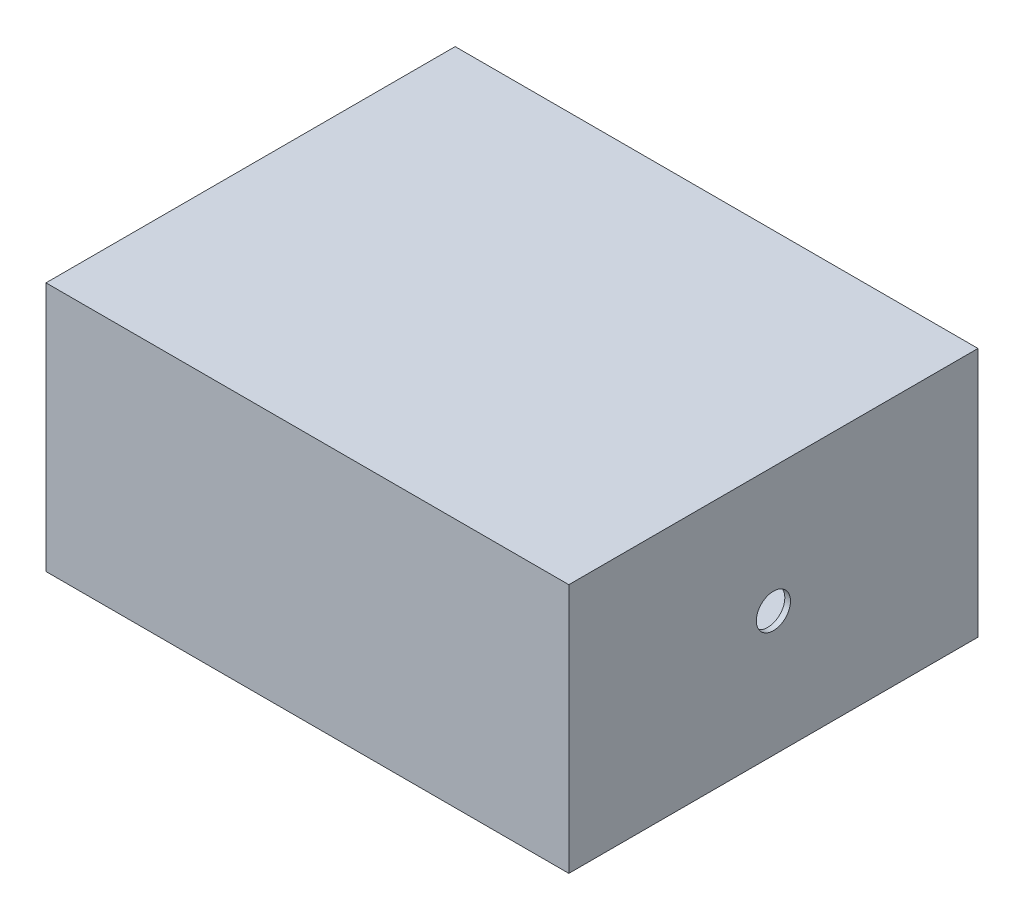
SolidWorks part; units mm, degrees
ref_plane "Front Plane" through (0, 0, 0) normal (0, 0, 1) x (1, 0, 0)
ref_plane "Top Plane" through (0, 0, 0) normal (0, 1, 0) x (1, 0, 0)
ref_plane "Right Plane" through (0, 0, 0) normal (1, 0, 0) x (0, 0, -1)
sketch "Sketch1" plane through (0, 0, 0) normal (0, 1, 0) x (1, 0, 0)
  line L1 (-460, 360) -> (460, 360)
  line L2 (-460, 360) -> (-460, -360)
  line L3 (-460, -360) -> (460, -360)
  line L4 (460, 360) -> (460, -360)
  line L5 (-460, 360) -> (460, -360) construction
  line L6 (-460, -360) -> (460, 360) construction
  point P0 (0, 0)
  dimension "D1" = 920
  dimension "D2" = 720
extrude "Boss-Extrude1" add sketch "Sketch1" along normal blind 440
shell "Shell1" thickness 10
sketch "Sketch2" plane through (460, 0, 0) normal (1, 0, 0) x (0, 0, -1)
  line L0 (0, 440) -> (0, 0) construction
  line L1 (-360, 440) -> (360, 440) construction
  line L2 (-360, 220) -> (360, 220) construction
  line L3 (-360, 440) -> (-360, 0) construction
  line L4 (360, 440) -> (360, 0) construction
  circle A0 centre (0, 220) radius 30.0753
extrude "Cut-Extrude1" cut sketch "Sketch2" against normal up to next
